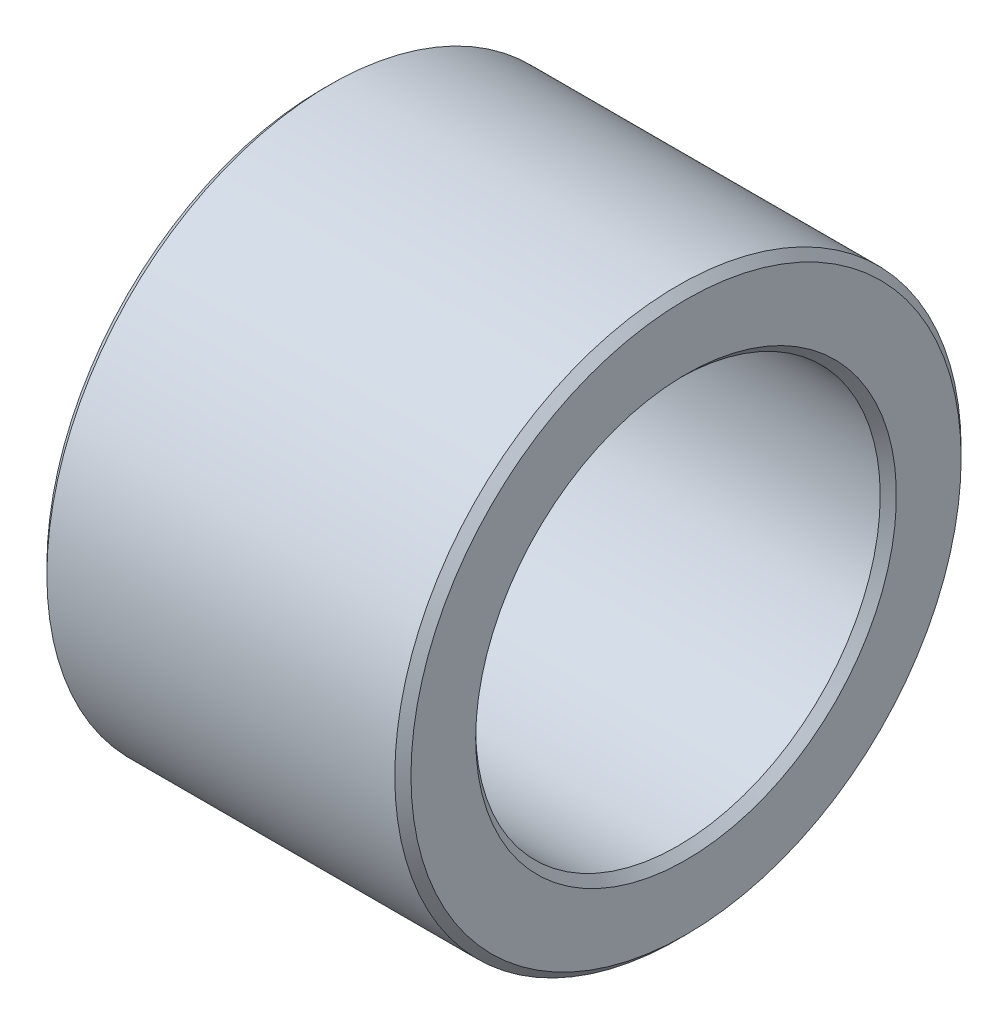
SolidWorks part; units mm, degrees
material "Простая углеродистая сталь"
ref_plane "Спереди  XY" through (0, 0, 0) normal (0, 0, 1) x (1, 0, 0)
ref_plane "Сверху  XZ" through (0, 0, 0) normal (0, 1, 0) x (1, 0, 0)
ref_plane "Справа  ZY" through (0, 0, 0) normal (1, 0, 0) x (0, 0, -1)
sketch "Эскиз1" plane through (0, 0, 0) normal (0, 0, 1) x (1, 0, 0)
  line L0 (0, 0) -> (9, 0) construction
  line L1 (0.2, 5) -> (8.8, 5)
  line L2 (9, 5.2) -> (9, 6.8)
  line L3 (8.8, 7) -> (0.2, 7)
  line L4 (0, 6.8) -> (0, 5.2)
  line L5 (0, 5.2) -> (0.2, 5)
  line L6 (0.2, 7) -> (0, 6.8)
  line L7 (9, 6.8) -> (8.8, 7)
  line L8 (8.8, 5) -> (9, 5.2)
  point P3 (0, 5)
  point P4 (9, 5)
  point P5 (0, 0)
  point P6 (9, 7)
  point P7 (0, 7)
  point P8 (0, 0)
  dimension "D1" = 9
  dimension "D2" = 5
  dimension "D3" = 7
revolve "Повернуть1" add sketch "Эскиз1" angle 360 about L0
